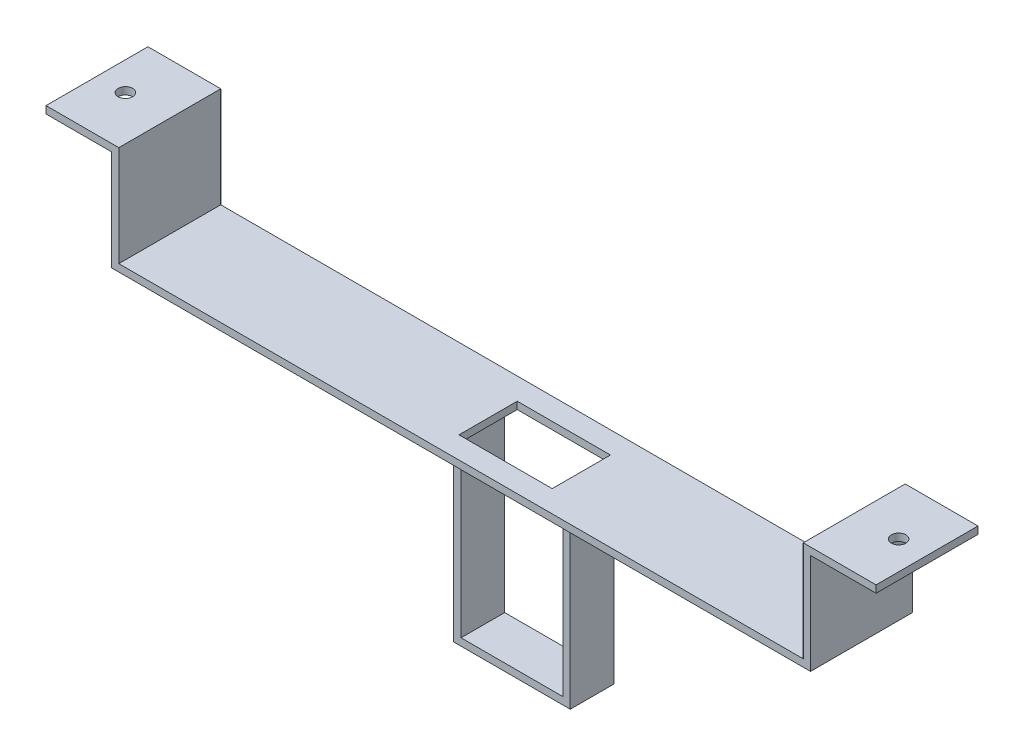
SolidWorks part; units mm, degrees
ref_plane "Front Plane" through (0, 0, 0) normal (0, 0, 1) x (1, 0, 0)
ref_plane "Top Plane" through (0, 0, 0) normal (0, 1, 0) x (1, 0, 0)
ref_plane "Right Plane" through (0, 0, 0) normal (1, 0, 0) x (0, 0, -1)
sketch "Sketch1" plane through (0, 0, 0) normal (0, 0, 1) x (1, 0, 0)
  line L0 (-117.5, -0.1042) -> (-117.5, 34.5)
  line L1 (-120, -2.5) -> (120, -2.5)
  line L2 (0, -2.5) -> (0, 22.8811) construction
  line L3 (117.5, 34.5) -> (142.5, 34.5)
  line L4 (-142.5, 34.5) -> (-117.5, 34.5)
  line L5 (-117.5, 0) -> (117.5, 0)
  line L7 (142.5, 34.5) -> (142.5, 32)
  line L8 (-120, -2.5) -> (-120, 32)
  line L12 (120, 32) -> (142.5, 32)
  line L13 (-120, 32) -> (-142.5, 32)
  line L14 (-142.5, 34.5) -> (-142.5, 32)
  line L17 (120, -2.5) -> (120, 32)
  line L18 (117.5, 0) -> (117.5, 34.5)
  point P0 (0, 0)
  dimension "D1" = 240
  dimension "D2" = 2.5
  dimension "D5" = 2.5
extrude "Boss-Extrude1" add sketch "Sketch1" along normal blind 35
sketch "Sketch2" plane through (0, 34.5, 0) normal (0, 1, 0) x (1, 0, 0)
  line L0 (0, 0) -> (0, -35) construction
  line L1 (-117.5, -35) -> (117.5, -35) construction
  line L2 (-117.5, -35) -> (-117.5, 0) construction
  line L3 (-8.2, -7.5) -> (23.8, -7.5)
  line L4 (-8.2, -7.5) -> (-8.2, -27.5)
  line L5 (-8.2, -27.5) -> (23.8, -27.5)
  line L6 (23.8, -7.5) -> (23.8, -27.5)
  line L7 (-117.5, -17.5) -> (-142.5, -17.5) construction
  line L8 (-117.5, -35) -> (-117.5, 0) construction
  line L9 (-142.5, -35) -> (-142.5, 0) construction
  circle A0 centre (-132.75, -17.5) radius 2.5
  circle A1 centre (132.75, -17.5) radius 2.5
  dimension "D1" = 15.25
  dimension "D3" = 5
  dimension "D2" = 20
  dimension "D4" = 32
  dimension "D5" = 109.3
extrude "Cut-Extrude1" cut sketch "Sketch2" against normal blind 90
ref_plane "Plane1" through (0, 0, 17.5) normal (0, 0, 1) x (1, 0, 0)
sketch "Sketch4" plane through (0, 0, 17.5) normal (0, 0, 1) x (1, 0, 0)
  line L0 (-120, -2.5) -> (120, -2.5) construction
  line L1 (-12.5, -2.5) -> (-12.5, -65)
  line L2 (-10, -2.5) -> (-10, -62.5)
  line L3 (-10, -62.5) -> (25, -62.5)
  line L4 (25, -2.5) -> (25, -62.5)
  line L5 (-12.5, -65) -> (27.5, -65)
  line L6 (27.5, -2.5) -> (27.5, -65)
  line L7 (-12.5, -2.5) -> (-10, -2.5)
  line L8 (-10, -2.5) -> (-9.6931, -2.0441)
  line L9 (25, -2.5) -> (27.5, -2.5)
  dimension "D1" = 35
  dimension "D2" = 10
  dimension "D3" = 60
  dimension "D4" = 2.5
extrude "Boss-Extrude2" add sketch "Sketch4" along normal mid plane 15 contours L2 L3 L4 L9 L6 L5 L1 L7
